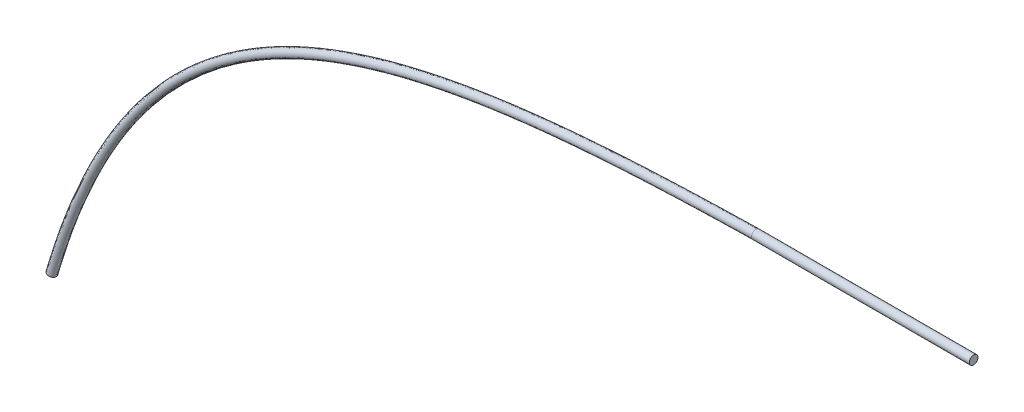
SolidWorks part; units mm, degrees
ref_plane "Front Plane" through (0, 0, 0) normal (0, 0, 1) x (1, 0, 0)
ref_plane "Top Plane" through (0, 0, 0) normal (0, 1, 0) x (1, 0, 0)
ref_plane "Right Plane" through (0, 0, 0) normal (1, 0, 0) x (0, 0, -1)
sketch "Sketch1" plane through (9.3567, 0.0005, 0) normal (-1, 0, 0) x (0, 0, 1)
  line L0 (8.2757, 22.8365) -> (16.9117, 22.8365) construction
  line L4 (8.2757, 27.1545) -> (8.2757, 18.5185)
  line L5 (8.2757, 18.5185) -> (16.9117, 18.5185)
  line L6 (16.9117, 18.5185) -> (16.9117, 27.1545)
  line L7 (16.9117, 27.1545) -> (8.2757, 27.1545)
  line L8 (8.2757, 27.1545) -> (8.2757, 18.5185)
  line L9 (8.2757, 18.5185) -> (16.9117, 18.5185)
  line L10 (16.9117, 18.5185) -> (16.9117, 27.1545)
  line L11 (16.9117, 27.1545) -> (8.2757, 27.1545)
  circle A0 centre (12.5937, 22.8365) radius 0.254
  dimension "D1" = 0
sketch "Sketch2" plane through (-15.9879, 15.9879, 0) normal (-0.7071, 0.7071, 0) x (0, 0, 1)
  line L4 (-20.7243, -18.9195) -> (-20.7243, -48.7645)
  line L5 (-20.7243, -48.7645) -> (37.2757, -48.7645)
  line L6 (37.2757, -48.7645) -> (37.2757, -18.9195)
  line L7 (37.2757, -18.9195) -> (-20.7243, -18.9195)
  line L8 (-20.7243, -18.9195) -> (-20.7243, -48.7645)
  line L9 (-20.7243, -48.7645) -> (37.2757, -48.7645)
  line L10 (37.2757, -48.7645) -> (37.2757, -18.9195)
  line L11 (37.2757, -18.9195) -> (-20.7243, -18.9195)
  dimension "D1" = 0
extrude "Extrude1" add sketch "Sketch1" against normal blind 12.7 contours A0 L0 | L0 A0
sketch "Sketch3" plane through (9.3567, 0.0005, 0) normal (-1, 0, 0) x (0, 0, 1)
  line L0 (12.5937, 23.0905) -> (12.5937, 22.5825) construction
  circle A0 centre (12.5937, 22.8365) radius 0.254 construction
  point P5 (12.5937, 22.8365)
ref_plane "Plane1" through (0, 0, 12.5937) normal (0, 0, -1) x (-1, 0, 0)
sketch "Sketch5" plane through (0, 0, 12.5937) normal (0, 0, -1) x (-1, 0, 0)
  spline S0 degree 3 poles (-9.3555, 22.8369) (12.1217, 22.415) (26.0071, 19.8971) (31.7034, 0.3581) knots 0 0 0 0 1 1 1 1
sketch "Sketch6" plane through (9.3567, 0.0005, 0) normal (-1, 0, 0) x (0, 0, 1)
  circle A0 centre (12.5937, 22.8365) radius 0.254
sweep "Sweep1" add profiles "Sketch6" path "Sketch5"
